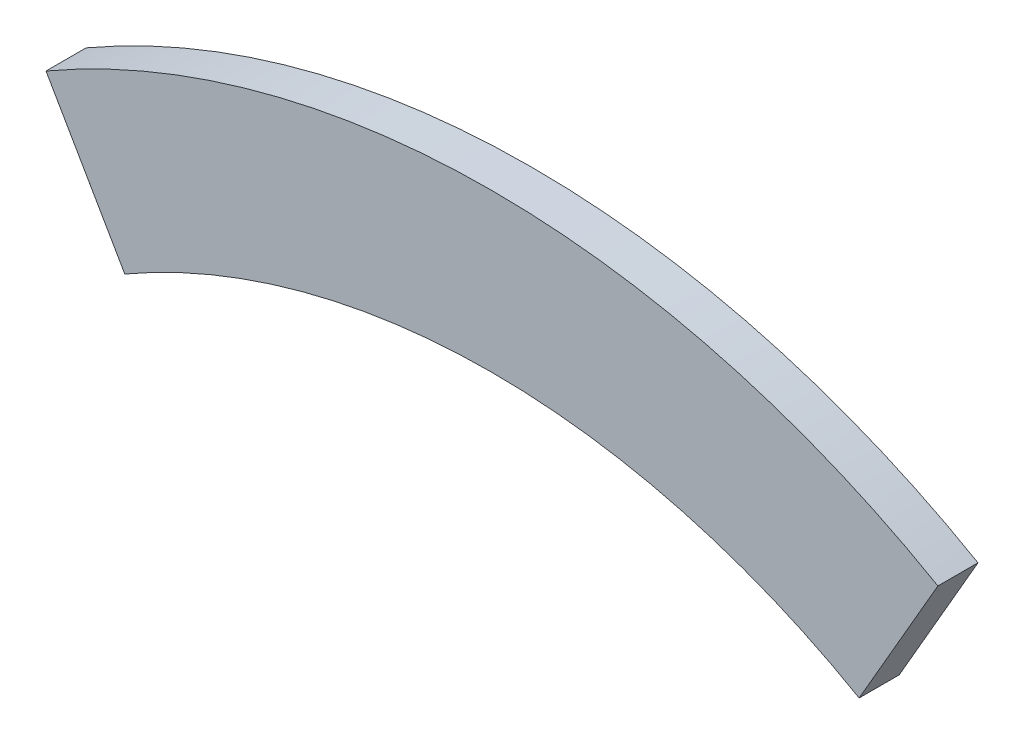
SolidWorks part; units mm, degrees
ref_plane "Front Plane" through (0, 0, 0) normal (0, 0, 1) x (1, 0, 0)
ref_plane "Top Plane" through (0, 0, 0) normal (0, 1, 0) x (1, 0, 0)
ref_plane "Right Plane" through (0, 0, 0) normal (1, 0, 0) x (0, 0, -1)
sketch "Sketch3" plane through (0, 0, 0) normal (0, 0, 1) x (1, 0, 0)
  line L4 (282.575, 489.4343) -> (232.664, 402.9859)
  line L6 (-232.664, 402.9859) -> (-282.575, 489.4343)
  arc A0 (282.575, 489.4343) -> (-282.575, 489.4343) centre (0, 0) ccw
  arc A1 (232.664, 402.9859) -> (-232.664, 402.9859) centre (0, 0) ccw
  circle A2 centre (0, 0) radius 565.15 construction
  circle A3 centre (0, 0) radius 465.328 construction
  point P13 (0, 465.328)
  dimension "D3" = 1130.3
  dimension "D7" = 60
  dimension "D4" = 99.822
extrude "Boss-Extrude1" add sketch "Sketch3" along normal blind 25.4
pattern_circular "CirPattern1" [suppressed] count 6 over 360
